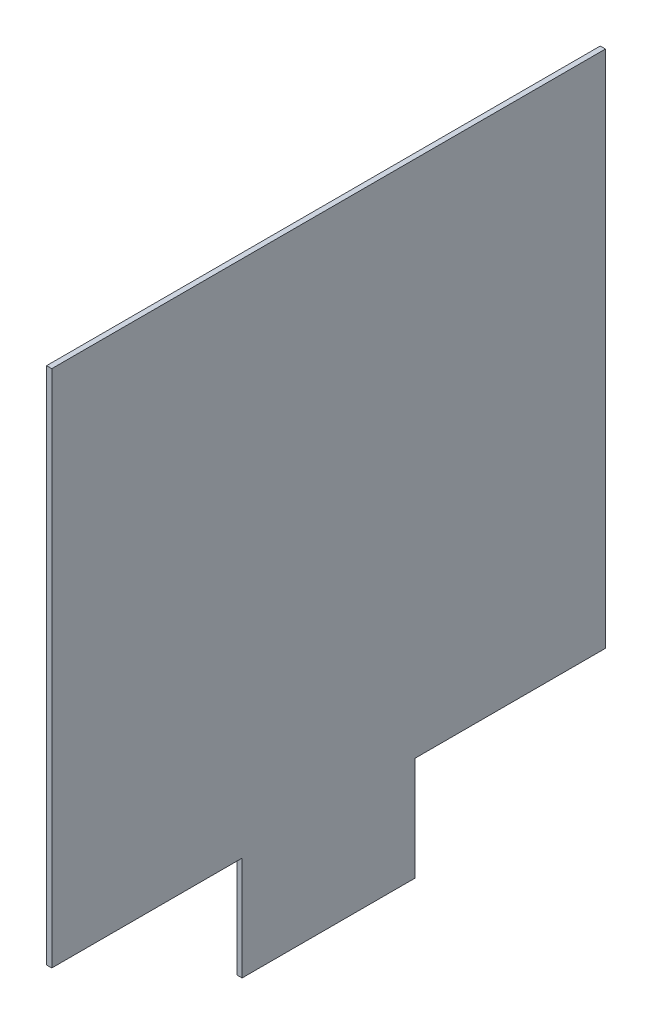
SolidWorks part; units mm, degrees
ref_plane "Front Plane" through (0, 0, 0) normal (0, 0, 1) x (1, 0, 0)
ref_plane "Top Plane" through (0, 0, 0) normal (0, 1, 0) x (1, 0, 0)
ref_plane "Right Plane" through (0, 0, 0) normal (1, 0, 0) x (0, 0, -1)
sketch "Sketch1" plane through (0, 0, 0) normal (1, 0, 0) x (0, 0, -1)
  line L0 (-151.2746, -55.7042) -> (-41.2746, -55.7042)
  line L1 (-41.2746, -115.7042) -> (58.7254, -115.7042)
  line L2 (-151.2746, -55.7042) -> (-151.2746, 244.2958)
  line L3 (-151.2746, 244.2958) -> (168.7254, 244.2958)
  line L4 (168.7254, -55.7042) -> (168.7254, 244.2958)
  line L5 (-38.4726, -55.7042) -> (168.7254, 244.2958) construction
  line L6 (-151.2746, 244.2958) -> (34.4935, -55.7042) construction
  line L7 (-41.2746, -55.7042) -> (-41.2746, -115.7042)
  line L8 (58.7254, -115.7042) -> (58.7254, -55.7042)
  line L9 (58.7254, -55.7042) -> (168.7254, -55.7042)
  point P0 (0, 0)
  dimension "D1" = 60
  dimension "D2" = 60
  dimension "D3" = 100
  dimension "D4" = 320
  dimension "D5" = 110
extrude "Boss-Extrude1" add sketch "Sketch1" along normal blind 3
